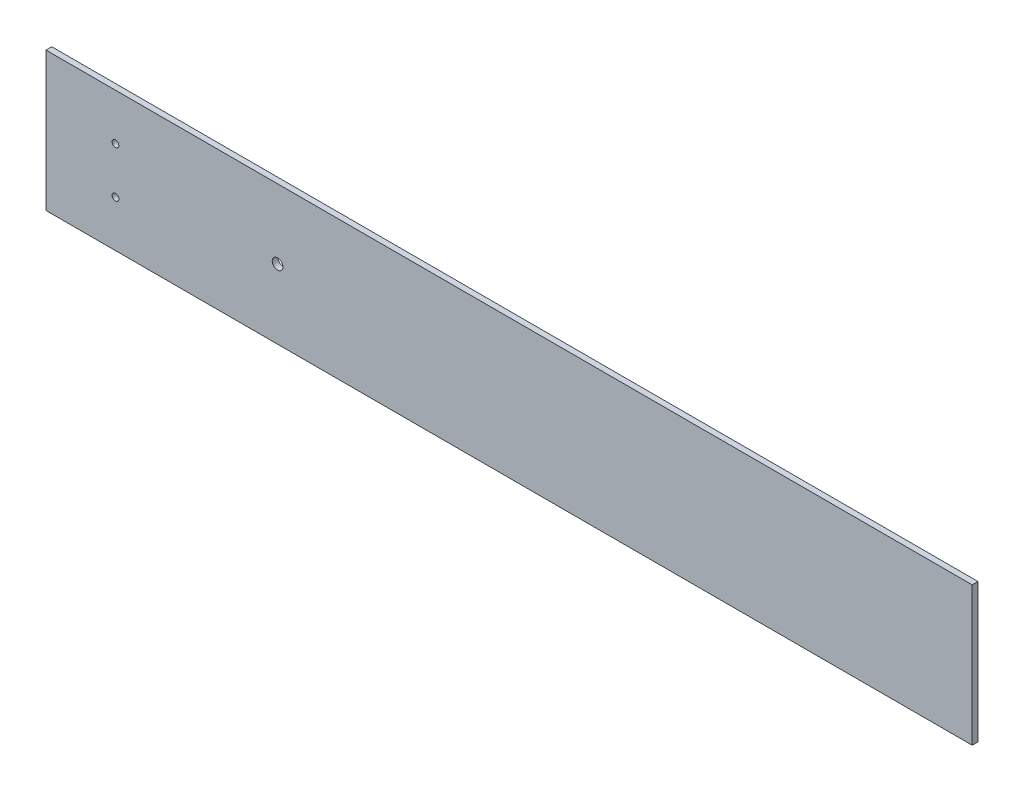
SolidWorks part; units mm, degrees
ref_plane "Front" through (0, 0, 0) normal (0, 0, 1) x (1, 0, 0)
ref_plane "Top" through (0, 0, 0) normal (0, 1, 0) x (1, 0, 0)
ref_plane "Right" through (0, 0, 0) normal (1, 0, 0) x (0, 0, -1)
sketch "Sketch1" plane through (0, 0, 0) normal (0, 0, 1) x (1, 0, 0)
  line L1 (0, 0) -> (508, 0)
  line L2 (0, 0) -> (0, 76.2)
  line L3 (0, 76.2) -> (508, 76.2)
  line L4 (508, 0) -> (508, 76.2)
  dimension "D1" = 508
  dimension "D2" = 76.2
extrude "basic_plank" add sketch "Sketch1" along normal blind 3.175
sketch "Sketch3" plane through (0, 0, 3.175) normal (0, 0, 1) x (1, 0, 0)
  line L0 (508, 76.2) -> (0, 76.2) construction
  line L1 (0, 76.2) -> (0, 0) construction
  line L2 (0, 38.1) -> (78.3618, 38.1) construction
  circle A0 centre (38.1, 50.8) radius 1.8415
  circle A1 centre (38.1, 25.4) radius 1.8415
  dimension "D1" = 3.683
  dimension "D2" = 25.4
  dimension "D3" = 38.1
extrude "Cut-Extrude4" cut sketch "Sketch3" against normal through all
sketch "Sketch4" plane through (0, 0, 3.175) normal (0, 0, 1) x (1, 0, 0)
  line L1 (0, 76.2) -> (0, 0) construction
  line L2 (508, 76.2) -> (0, 76.2) construction
  circle A0 centre (127, 38.1) radius 2.921
  dimension "D1" = 5.842
  dimension "D2" = 127
  dimension "D3" = 38.1
extrude "through_tripod" cut sketch "Sketch4" against normal through all
